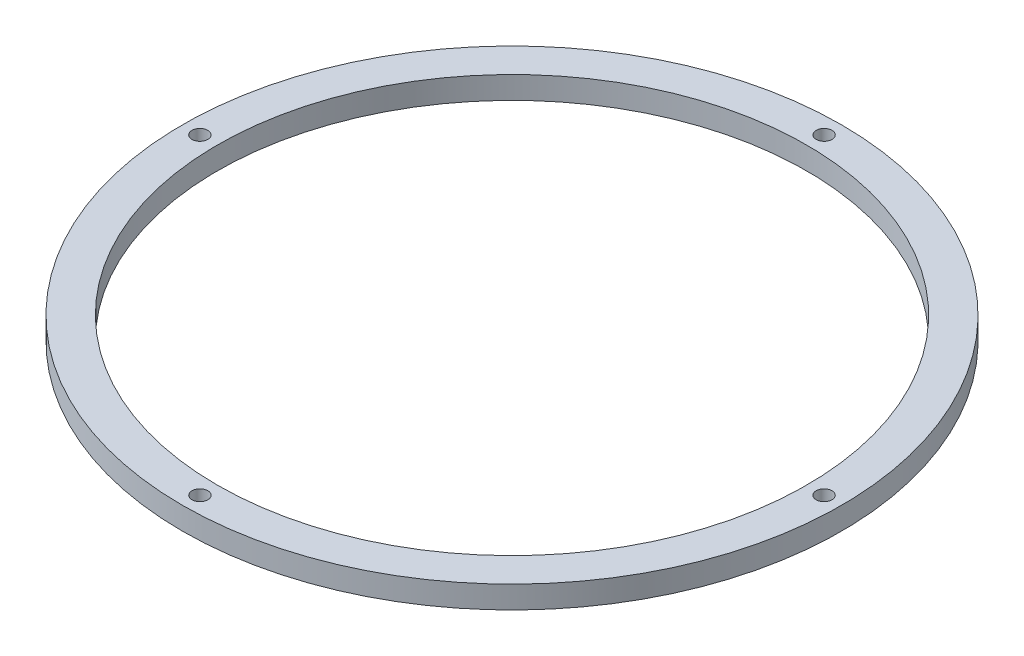
SolidWorks part; units mm, degrees
ref_plane "Front Plane" through (0, 0, 0) normal (0, 0, 1) x (1, 0, 0)
ref_plane "Top Plane" through (0, 0, 0) normal (0, 1, 0) x (1, 0, 0)
ref_plane "Right Plane" through (0, 0, 0) normal (1, 0, 0) x (0, 0, -1)
sketch "Sketch1" plane through (0, 0, 0) normal (0, 1, 0) x (1, 0, 0)
  circle A0 centre (0, 0) radius 125
  circle A1 centre (0, 0) radius 111.75
  dimension "D1" = 250
  dimension "D2" = 223.5
extrude "Boss-Extrude1" add sketch "Sketch1" along normal blind 8.5
sketch "Sketch2" plane through (0, 8.5, 0) normal (0, 1, 0) x (1, 0, 0)
  line L0 (0, 0) -> (0, 143.5609) construction
  circle A0 centre (0, 118.375) radius 3
  circle A1 centre (118.375, 0) radius 3
  circle A2 centre (0, -118.375) radius 3
  circle A3 centre (-118.375, 0) radius 3
  circle A4 centre (0, 0) radius 118.375 construction
  dimension "D1" = 6
  dimension "D2" = 6
  dimension "D3" = 6
  dimension "D4" = 6
  dimension "D5" = 236.75
extrude "Cut-Extrude1" cut sketch "Sketch2" against normal through all contours A2 | A3 | A1 | A0
